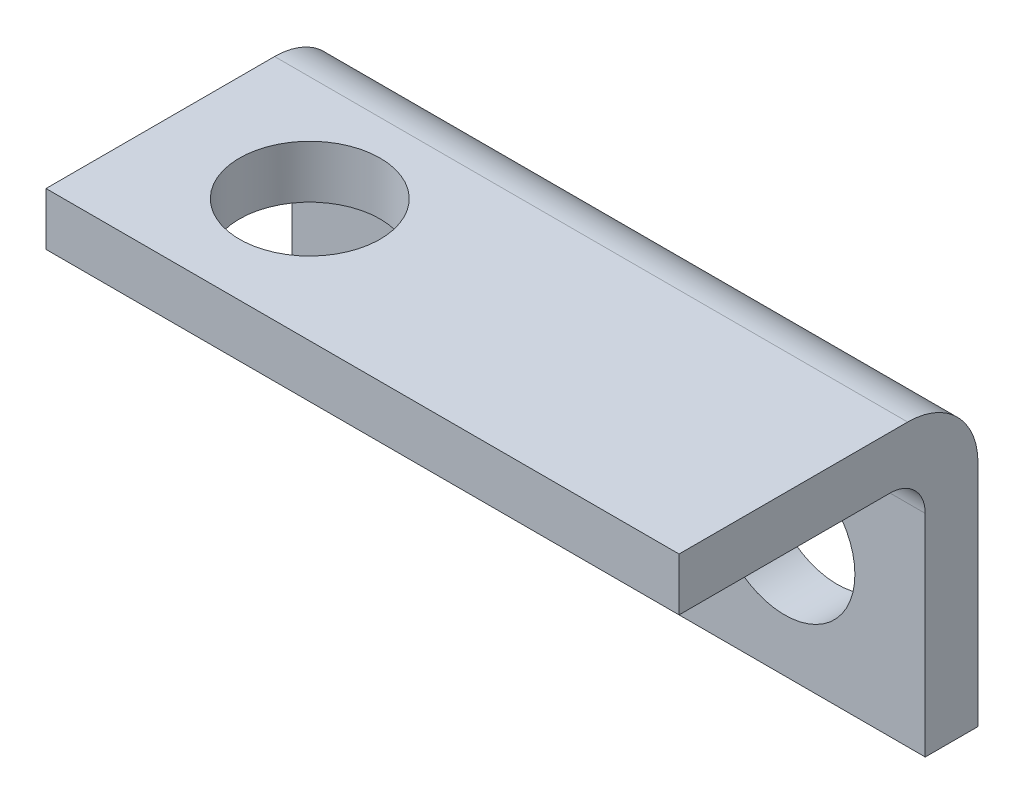
SolidWorks part; units mm, degrees
ref_plane "Płaszczyzna XY" through (0, 0, 0) normal (0, 0, 1) x (1, 0, 0)
ref_plane "Płaszczyzna XZ" through (0, 0, 0) normal (0, 1, 0) x (1, 0, 0)
ref_plane "Płaszczyzna YZ" through (0, 0, 0) normal (1, 0, 0) x (0, 0, -1)
sketch "Sketch1" plane through (0, 0, 0) normal (0, 0, 1) x (1, 0, 0)
  line L1 (-18, 8.5) -> (18, 8.5)
  line L2 (-18, 8.5) -> (-18, -8.5)
  line L3 (-18, -8.5) -> (18, -8.5)
  line L4 (18, 8.5) -> (18, -8.5)
  line L5 (-18, 8.5) -> (18, -8.5) construction
  line L6 (-18, -8.5) -> (18, 8.5) construction
  point P0 (0, 0)
  dimension "D1" = 36
  dimension "D2" = 17
extrude "Boss-Extrude1" add sketch "Sketch1" along normal blind 3
sketch "Sketch15" plane through (0, 0, 3) normal (0, 0, 1) x (1, 0, 0)
  line L0 (-18, 8.5) -> (-18, -8.5) construction
  line L1 (-18, 8.5) -> (-18, 5.5)
  line L2 (18, 8.5) -> (-18, 8.5) construction
  line L3 (18, 8.5) -> (-18, 8.5)
  line L4 (18, -8.5) -> (18, 8.5) construction
  line L5 (18, 5.5) -> (18, 8.5)
  line L6 (-18, 5.5) -> (18, 5.5)
  dimension "D1" = 3
extrude "Boss-Extrude2" add sketch "Sketch15" along normal blind 14
fillet "Fillet2" radius 2 1 edges at (0, 5.5, 3)
fillet "Fillet3" radius 4 1 edges at (0, 8.5, 0)
sketch "Sketch17" plane through (0, -8.5, 0) normal (0, -1, 0) x (1, 0, 0)
  line L0 (-18, 0) -> (18, 0) construction
  line L2 (-18, 17) -> (-18, 5) construction
  circle A0 centre (-10, 10) radius 4
  dimension "D1" = 8
  dimension "D2" = 10
  dimension "D3" = 8
extrude "Cut-Extrude1" cut sketch "Sketch17" against normal through all
sketch "Sketch18" plane through (0, 0, 17) normal (0, 0, 1) x (1, 0, 0)
  line L0 (18, 8.5) -> (-18, 8.5) construction
  line L2 (18, -8.5) -> (18, 3.5) construction
  circle A0 centre (10, -1.5) radius 4
  dimension "D1" = 8
  dimension "D2" = 10
  dimension "D3" = 8
extrude "Cut-Extrude2" cut sketch "Sketch18" against normal through all
